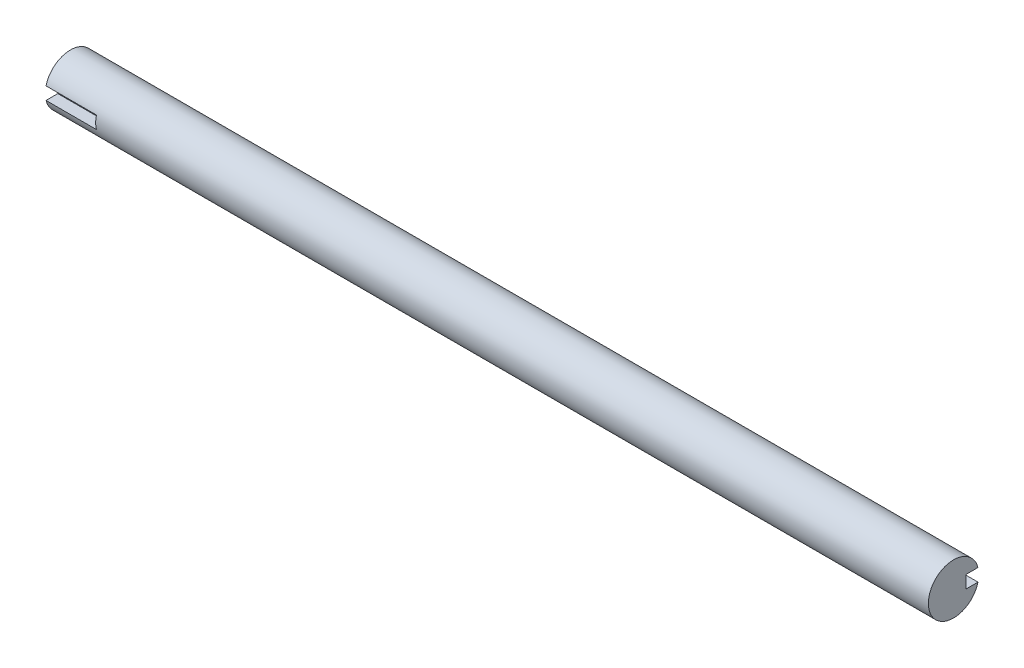
SolidWorks part; units mm, degrees
ref_plane "Front Plane" through (0, 0, 0) normal (0, 0, 1) x (1, 0, 0)
ref_plane "Top Plane" through (0, 0, 0) normal (0, 1, 0) x (1, 0, 0)
ref_plane "Right Plane" through (0, 0, 0) normal (1, 0, 0) x (0, 0, -1)
sketch "Sketch1" plane through (0, 0, 0) normal (1, 0, 0) x (0, 0, -1)
  circle A0 centre (0, 0) radius 10
  dimension "20" = 20
extrude "Boss-Extrude1" add sketch "Sketch1" along normal blind 350
sketch "Sketch2" plane through (0, 0, 0) normal (-1, 0, 0) x (0, 0, 1)
  line L1 (5, -2.5) -> (15, -2.5)
  line L2 (5, -2.5) -> (5, 2.5)
  line L3 (5, 2.5) -> (15, 2.5)
  line L4 (15, -2.5) -> (15, 2.5)
  line L5 (5, -2.5) -> (15, 2.5) construction
  line L6 (5, 2.5) -> (15, -2.5) construction
  circle A0 centre (0, 0) radius 10 construction
  point P0 (10, 0)
  dimension "D1" = 5
  dimension "D2" = 10
extrude "Cut-Extrude1" cut sketch "Sketch2" against normal blind 20 contours L4 L3 L2 L1
sketch "Sketch3" plane through (350, 0, 0) normal (1, 0, 0) x (0, 0, -1)
  line L1 (5, 2.5) -> (15, 2.5)
  line L2 (5, 2.5) -> (5, -2.5)
  line L3 (5, -2.5) -> (15, -2.5)
  line L4 (15, 2.5) -> (15, -2.5)
  line L5 (5, 2.5) -> (15, -2.5) construction
  line L6 (5, -2.5) -> (15, 2.5) construction
  circle A0 centre (0, 0) radius 10 construction
  point P0 (10, 0)
  dimension "D1" = 5
  dimension "1" = 10
extrude "Cut-Extrude2" cut sketch "Sketch3" against normal blind 20 contours L4 L3 L2 L1
